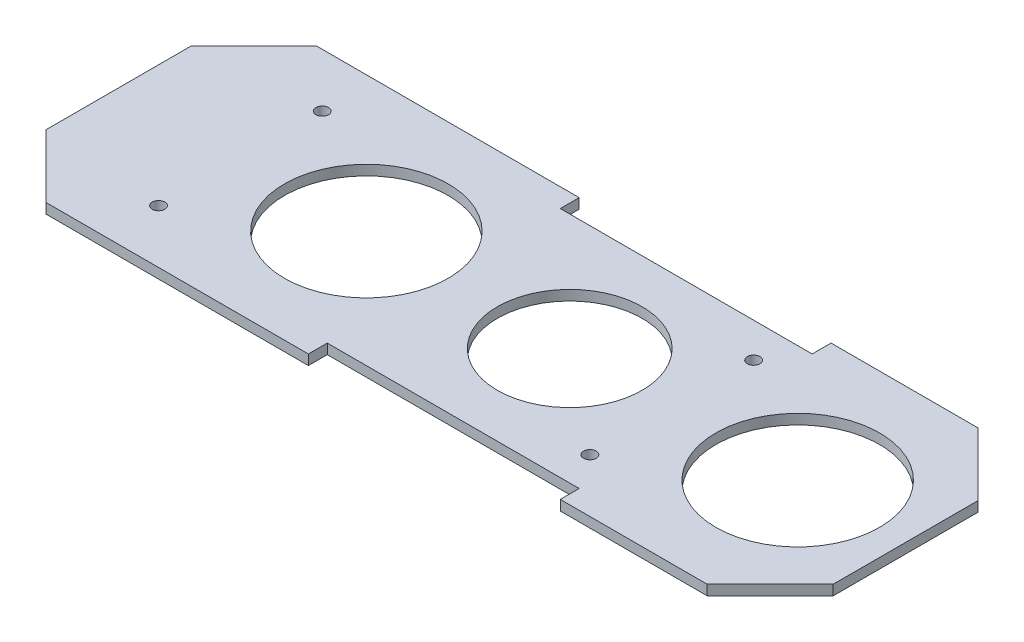
SolidWorks part; units mm, degrees
ref_plane "Front Plane" through (0, 0, 0) normal (0, 0, 1) x (1, 0, 0)
ref_plane "Top Plane" through (0, 0, 0) normal (0, 1, 0) x (1, 0, 0)
ref_plane "Right Plane" through (0, 0, 0) normal (1, 0, 0) x (0, 0, -1)
sketch "Sketch2" plane through (0, 0, 0) normal (0, 1, 0) x (1, 0, 0)
  line L0 (0, 0) -> (162.4584, 0) construction
  line L1 (0, 21.5) -> (51.6667, 21.5)
  line L2 (0, 21.5) -> (0, -21.5)
  line L3 (0, -21.5) -> (51.6667, -21.5)
  line L4 (125, 21.5) -> (125, -21.5)
  line L5 (51.6667, -18.5) -> (91.6667, -18.5)
  line L6 (51.6667, 21.5) -> (91.6667, 21.5) construction
  line L7 (51.6667, 21.5) -> (51.6667, 18.5)
  line L8 (51.6667, 18.5) -> (91.6667, 18.5)
  line L9 (91.6667, 21.5) -> (91.6667, 18.5)
  line L10 (91.6667, -21.5) -> (91.6667, -18.5)
  line L11 (51.6667, -21.5) -> (91.6667, -21.5) construction
  line L12 (51.6667, -21.5) -> (51.6667, -18.5)
  line L13 (51.6667, 21.5) -> (91.6667, 21.5) construction
  line L14 (91.6667, 21.5) -> (125, 21.5)
  line L15 (51.6667, -21.5) -> (91.6667, -21.5) construction
  line L16 (91.6667, -21.5) -> (125, -21.5)
  circle A0 centre (19.37, 13) radius 1
  circle A1 centre (87.87, 13) radius 1
  circle A2 centre (87.87, -13) radius 1
  circle A3 centre (19.37, -13) radius 1
  circle A4 centre (39.37, 0) radius 13
  circle A5 centre (107.87, 0) radius 13
  circle A6 centre (71.6667, 0) radius 11.5
  point P4 (0, 0)
  point P33 (71.6667, -18.5)
  dimension "D6" = 37.13
  dimension "D8" = 2
  dimension "D9" = 2
  dimension "D11" = 26
  dimension "D12" = 26
  dimension "D15" = 23
  dimension "D1" = 125
  dimension "D2" = 43
  dimension "D3" = 3
  dimension "D4" = 40
  dimension "D5" = 33.3333
  dimension "D7" = 68.5
  dimension "D10" = 13
  dimension "D13" = 20
  dimension "D14" = 20
extrude "Boss-Extrude1" add sketch "Sketch2" along normal blind 1.6 contours L2 L0 A4 A6 A5 L4 L1 L9 L8 L7 A0 A1 | L0 L2 L3 L12 L5 L10 L4 A5 A6 A4 A2 A3
chamfer "Chamfer1" distance 10 angle 45 4 edges at (0, 0.8, 21.5) (0, 0.8, -21.5) (125, 0.8, -21.5) (125, 0.8, 21.5)
